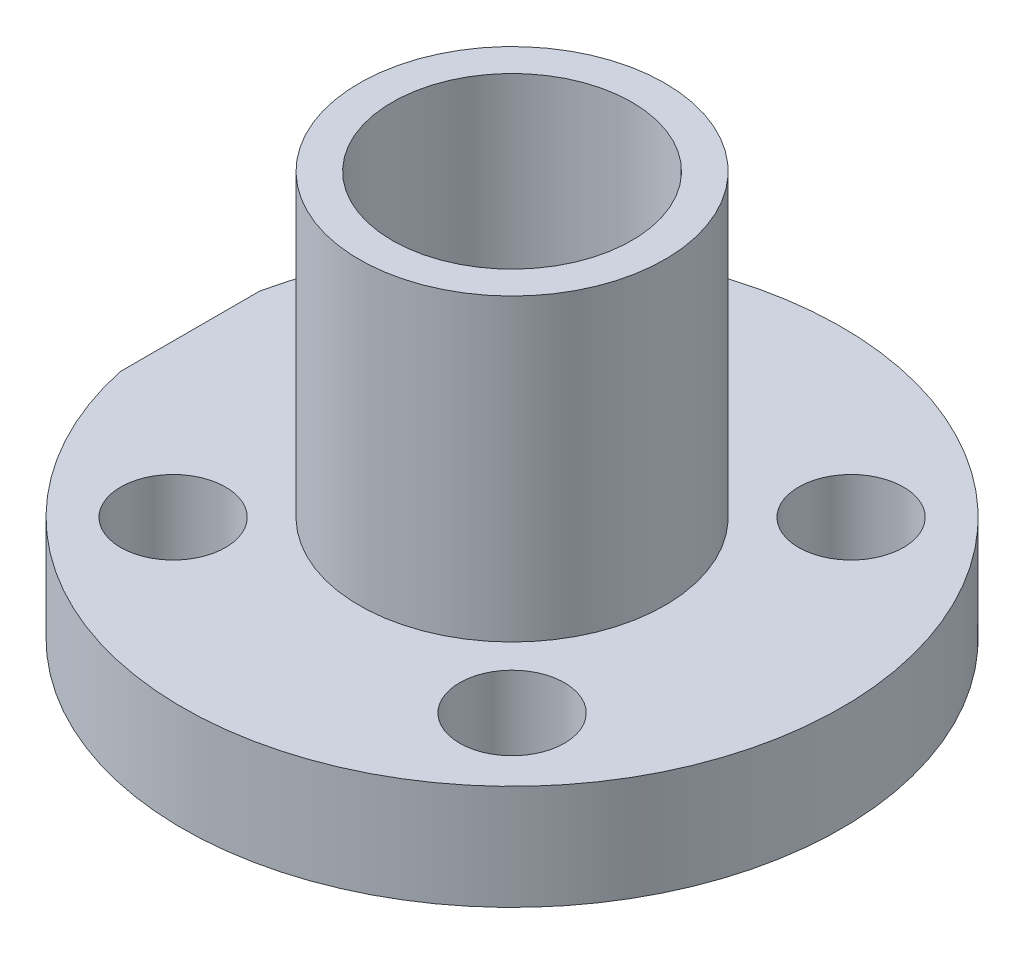
SolidWorks part; units mm, degrees
material "Messing"
ref_plane "Ebene vorne" through (0, 0, 0) normal (0, 0, 1) x (1, 0, 0)
ref_plane "Ebene oben" through (0, 0, 0) normal (0, 1, 0) x (1, 0, 0)
ref_plane "Ebene rechts" through (0, 0, 0) normal (1, 0, 0) x (0, 0, -1)
sketch "Skizze1" plane through (0, 0, 0) normal (0, 0, 1) x (1, 0, 0)
  line L0 (0, 0) -> (0, 10.6853) construction
  line L1 (-4, 0) -> (-4, 13.5)
  line L2 (-4, 13.5) -> (-5.1, 13.5)
  line L3 (-5.1, 13.5) -> (-5.1, 3.5)
  line L4 (-5.1, 3.5) -> (-11, 3.5)
  line L5 (-11, 3.5) -> (-11, 0)
  line L6 (-11, 0) -> (-5.1, 0)
  line L7 (-5.1, 0) -> (-5.1, -1.5)
  line L8 (-5.1, -1.5) -> (-4, -1.5)
  line L9 (-4, -1.5) -> (-4, 0)
  point P11 (0, 0)
  dimension "D1" = 10
  dimension "D2" = 3.5
  dimension "D3" = 1.5
  dimension "D4" = 5.1
  dimension "D5" = 8
  dimension "D6" = 11
revolve "Rotation1" add sketch "Skizze1" angle 360 about L0
hole_wizard "Ø3.5 (3.5) Durchmesser Bohrung1" positions "Skizze3" profile "Skizze4" hole size "Ø3.5" standard "DIN" end condition through all
sketch "Skizze3" plane through (0, 3.5, 0) normal (0, 1, 0) x (1, 0, 0)
  line L8 (-5.6569, 5.6569) -> (5.6569, 5.6569) construction
  line L9 (-5.6569, 5.6569) -> (-5.6569, -5.6569) construction
  line L10 (-5.6569, -5.6569) -> (5.6569, -5.6569) construction
  line L11 (5.6569, 5.6569) -> (5.6569, -5.6569) construction
  circle A0 centre (0, 0) radius 8 construction
  point P80 (-5.6569, 5.6569)
  point P81 (5.6569, -5.6569)
  point P84 (-5.6569, -5.6569)
  point P85 (5.6569, 5.6569)
  dimension "D1" = 16
sketch "Skizze4" plane through (5.6569, 3.5, -5.6569) normal (1, 0, 0) x (0, 0, 1)
  line L0 (0, 0) -> (0, 5)
  line L1 (0, 5) -> (1.75, 5)
  line L2 (1.75, 5) -> (1.75, 0)
  line L5 (1.75, 0) -> (0, 0)
  line L11 (0, -6.35) -> (0, 107.95) construction
  dimension "Bohrerdurchmesser" = 3.5
  dimension "Bohrungstiefe" = 5
sketch "Skizze5" plane through (0, 3.5, 0) normal (0, 1, 0) x (1, 0, 0)
  line L0 (-11, 0) -> (0, 0) construction
  line L1 (-11.25, -25) -> (-10.75, -25)
  line L2 (-11.25, -25) -> (-11.25, 25)
  line L3 (-11.25, 25) -> (-10.75, 25)
  line L4 (-10.75, -25) -> (-10.75, 25)
  line L5 (-11.25, -25) -> (-10.75, 25) construction
  line L6 (-11.25, 25) -> (-10.75, -25) construction
  circle A0 centre (0, 0) radius 11 construction
  point P0 (-11, 0)
  dimension "D1" = 50
  dimension "D2" = 0.5
extrude "Schnitt-Linear austragen1" cut sketch "Skizze5" against normal through all
